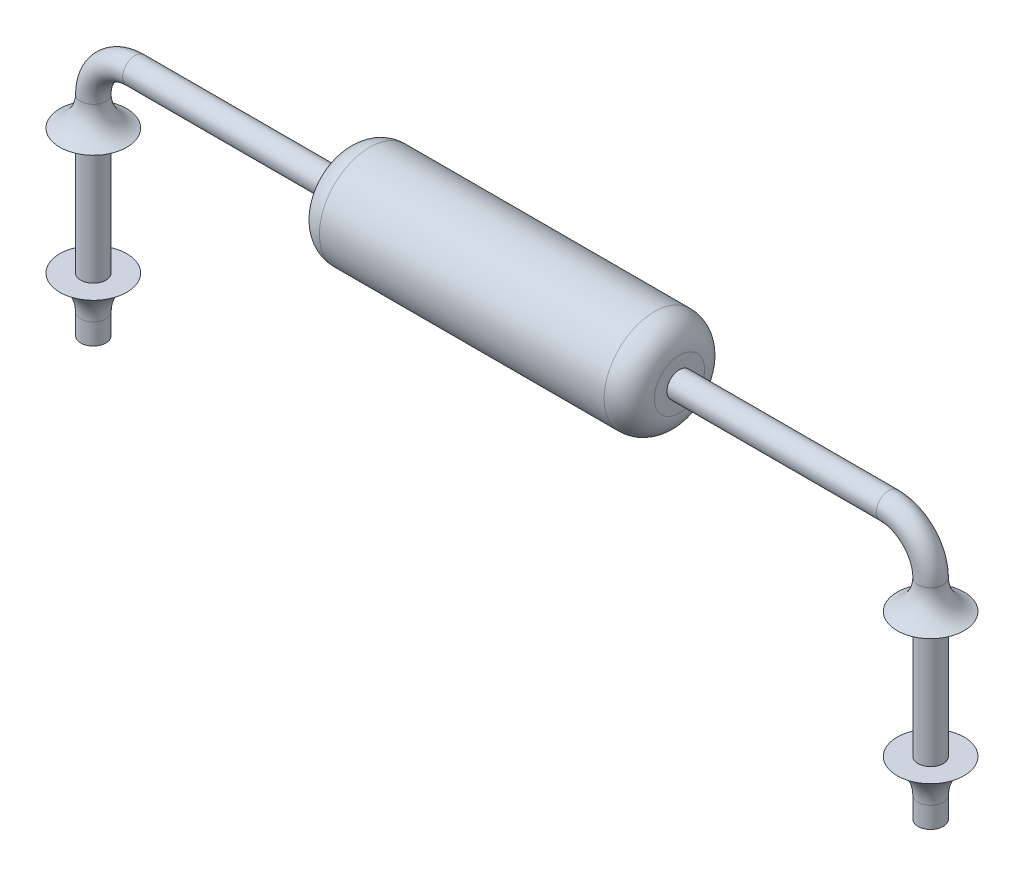
SolidWorks part; units mm, degrees
ref_plane "Front" through (0, 0, 0) normal (0, 0, 1) x (1, 0, 0)
ref_plane "Top" through (0, 0, 0) normal (0, 1, 0) x (1, 0, 0)
ref_plane "Right" through (0, 0, 0) normal (1, 0, 0) x (0, 0, -1)
sketch "Sketch1" plane through (0, 0, 0) normal (0, 0, 1) x (1, 0, 0)
  line L0 (-19.9518, 0) -> (19.9518, 0) construction
  line L1 (1.75, 0) -> (-1.75, 0)
  line L2 (-1.75, 0.35) -> (1.75, 0.35)
  line L3 (-1.75, 0.35) -> (-1.75, 0)
  line L5 (1.75, 0.35) -> (1.75, 0)
  dimension "D1" = 1.75
  dimension "D2" = 0.35
  dimension "D3" = 3.5
revolve "Base-Revolve" add sketch "Sketch1" angle 360 about L0
fillet "Fillet1" radius 0.1 2 edges at (1.75, 0, 0.35) (-1.75, 0, 0.35)
sketch "Sketch2" plane through (0, 0, 0) normal (0, 0, 1) x (1, 0, 0)
  line L0 (0.15, 0) -> (0.15, 0.55)
  line L1 (-19.9518, 0) -> (19.9518, 0) construction
  line L2 (0.15, 0.55) -> (1.25, 0.55)
  line L3 (1.25, 0.55) -> (1.25, 0)
  line L4 (1.25, 0) -> (0.15, 0)
  line L5 (0, 0) -> (1.5054, 0) construction
  line L6 (1.75, -0.25) -> (1.75, 0.25) construction
  dimension "D1" = 1.1
  dimension "D2" = 0.55
  dimension "D3" = 0.5
revolve "Boss-Revolve1" add sketch "Sketch2" angle 360 about L5
sketch "Sketch3" plane through (0, 0, 0) normal (1, 0, 0) x (0, 0, -1)
  circle A0 centre (0, -7) radius 0.15
  dimension "D1" = 0.3
  dimension "D2" = 7
sketch "Sketch4" plane through (0, 0, 0) normal (0, 0, 1) x (1, 0, 0)
  line L0 (0, -7) -> (-4.5, -7)
  line L1 (-5, -6.5) -> (-5, -0.5)
  line L2 (-4.5, 0) -> (4.5, 0)
  line L3 (-19.9518, 0) -> (19.9518, 0) construction
  line L4 (5, -0.5) -> (5, -6.5)
  line L5 (4.5, -7) -> (0, -7)
  arc A0 (-5, -0.5) -> (-4.5, 0) centre (-4.5, -0.5) cw
  arc A1 (5, -0.5) -> (4.5, 0) centre (4.5, -0.5) ccw
  arc A2 (4.5, -7) -> (5, -6.5) centre (4.5, -6.5) ccw
  arc A3 (-5, -6.5) -> (-4.5, -7) centre (-4.5, -6.5) ccw
  point P12 (5, 0)
  dimension "D4" = 0.5
  dimension "D2" = 10
  dimension "D3" = 7
sweep "Boss-Sweep1" add profiles "Sketch3" path "Sketch4"
sketch "Sketch5" plane through (0, 0, 0) normal (0, 0, 1) x (1, 0, 0)
  line L0 (2, 0) -> (-2.5573, 0) construction
  line L1 (-1.7, 0.6) -> (1.7, 0.6)
  line L2 (-2, 0.3) -> (-2, 0)
  line L3 (-2, 0) -> (-1.955, 0)
  line L4 (2, 0.3) -> (2, 0)
  line L5 (1.75, 0) -> (4.5, 0) construction
  line L6 (-1.955, 0.3) -> (-1.955, 0)
  line L7 (1.955, 0) -> (2, 0)
  line L8 (1.955, 0.3) -> (1.955, 0)
  line L9 (-1.7, 0.555) -> (1.7, 0.555)
  arc A0 (-2, 0.3) -> (-1.7, 0.6) centre (-1.7, 0.3) cw
  arc A1 (2, 0.3) -> (1.7, 0.6) centre (1.7, 0.3) ccw
  arc A2 (1.955, 0.3) -> (1.7, 0.555) centre (1.7, 0.3) ccw
  arc A3 (-1.955, 0.3) -> (-1.7, 0.555) centre (-1.7, 0.3) cw
  dimension "D4" = 0.3
  dimension "D5" = 0.3
  dimension "D1" = 2
  dimension "D2" = 2
  dimension "D3" = 0.6
  dimension "D6" = 0.045
revolve "Boss-Revolve2" add sketch "Sketch5" angle 360 about L0
sketch "Sketch6" plane through (0, 0, 0) normal (0, 0, 1) x (1, 0, 0)
  line L1 (-6, -3) -> (6, -3)
  line L2 (-6, -3) -> (-6, -8)
  line L3 (-6, -8) -> (6, -8)
  line L4 (6, -3) -> (6, -8)
  line L5 (-6, -0.85) -> (6, -0.85) construction
  line L6 (-6, -0.85) -> (-6, -2.35) construction
  line L7 (-6, -2.35) -> (6, -2.35) construction
  line L8 (6, -0.85) -> (6, -2.35) construction
  line L9 (-6, -0.85) -> (6, -2.35) construction
  line L10 (-6, -2.35) -> (6, -0.85) construction
  point P4 (0, -1.6)
  dimension "D1" = 3
  dimension "D2" = 5
  dimension "D3" = 12
  dimension "D4" = 6
  dimension "D5" = 1.5
  dimension "D6" = 0.85
extrude "Cut-Extrude1" cut sketch "Sketch6" against normal through all and the other way through all
sketch "Sketch7" plane through (0, 0, 0) normal (0, 0, 1) x (1, 0, 0)
  line L0 (6, -0.85) -> (6, -2.35) construction
  line L1 (-6, -0.85) -> (6, -2.35) construction
  line L2 (-6, -2.35) -> (6, -0.85) construction
  line L3 (-6, -2.35) -> (6, -2.35) construction
  line L4 (-6, -0.85) -> (-6, -2.35) construction
  line L5 (-6, -0.85) -> (6, -0.85) construction
  line L6 (6, -0.85) -> (6, -2.35) construction
  line L7 (-6, -0.85) -> (6, -2.35) construction
  line L8 (-6, -2.35) -> (6, -0.85) construction
  line L9 (-6, -2.35) -> (6, -2.35) construction
  line L10 (-6, -0.85) -> (-6, -2.35) construction
  line L11 (-6, -0.85) -> (6, -0.85) construction
  line L12 (-5, -0.5) -> (-5, -3) construction
  line L13 (-4.85, -0.5) -> (-5.15, -0.5) construction
  line L14 (-6, -3) -> (6, -3) construction
  line L15 (-5.15, -0.85) -> (-5.4, -0.85)
  line L16 (-5.15, -0.5) -> (-5.15, -3) construction
  line L17 (-5.15, -0.85) -> (-5.15, -0.5)
  line L18 (-5.15, -2.35) -> (-5.15, -2.75)
  line L19 (-5.15, -2.35) -> (-5.4, -2.35)
  arc A0 (-5.4, -0.85) -> (-5.15, -0.5) centre (-5.52, -0.5) ccw
  arc A1 (-5.4, -2.35) -> (-5.15, -2.75) centre (-5.595, -2.75) cw
  dimension "D1" = 0.25
  dimension "D2" = 0.4
revolve "Revolve1" add sketch "Sketch7" angle 360 about L12
sketch "Sketch8" plane through (0, 0, 0) normal (0, 0, 1) x (1, 0, 0)
  line L0 (5, -0.5) -> (5, -3) construction
  line L1 (4.85, -0.5) -> (5.15, -0.5) construction
  line L2 (4.85, -3) -> (5.15, -3) construction
  line L3 (5.15, -0.85) -> (5.4, -0.85)
  line L4 (5.15, -3) -> (5.15, -0.5) construction
  line L5 (5.15, -2.35) -> (5.4, -2.35)
  line L6 (5.15, -2.35) -> (5.15, -2.75)
  line L7 (5.15, -0.85) -> (5.15, -0.5)
  line L8 (-5.4, -0.85) -> (-4.6, -0.85) construction
  line L9 (-4.6, -2.35) -> (-5.4, -2.35) construction
  arc A0 (5.4, -0.85) -> (5.15, -0.5) centre (5.52, -0.5) cw
  arc A1 (5.4, -2.35) -> (5.15, -2.75) centre (5.595, -2.75) ccw
  dimension "D1" = 0.25
  dimension "D2" = 0.4
revolve "Revolve2" add sketch "Sketch8" angle 360 about L0
